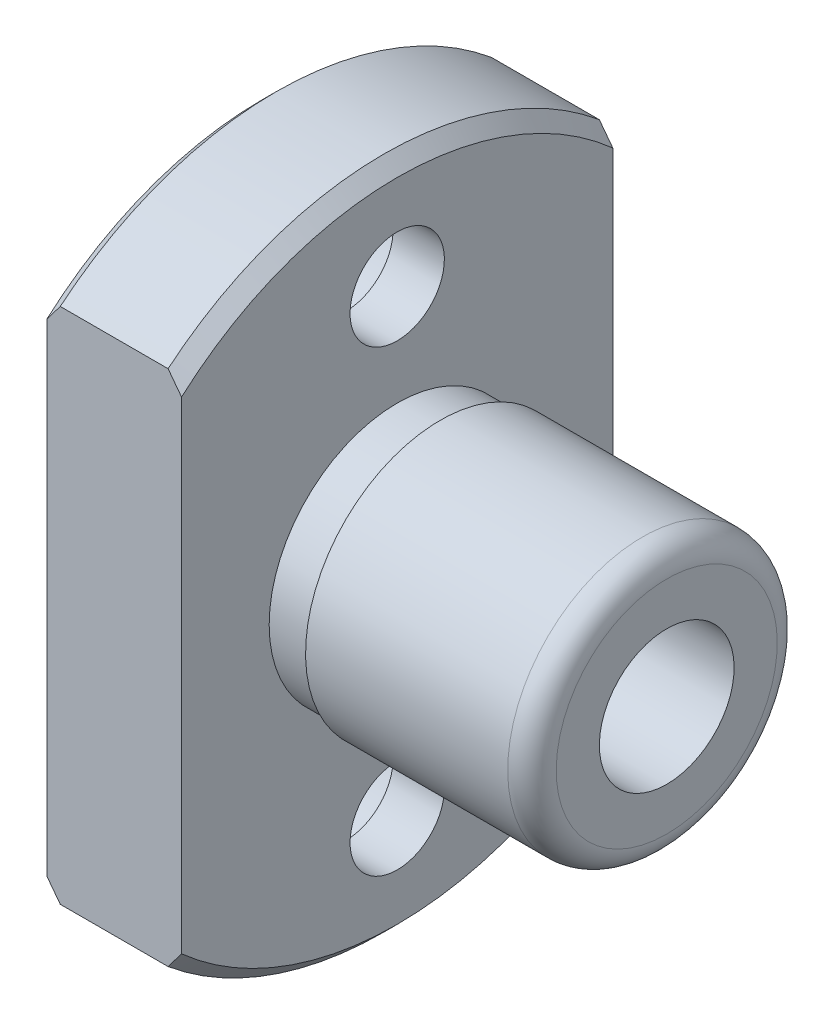
SolidWorks part; units mm, degrees
ref_plane "Front Plane" through (0, 0, 0) normal (0, 0, 1) x (1, 0, 0)
ref_plane "Top Plane" through (0, 0, 0) normal (0, 1, 0) x (1, 0, 0)
ref_plane "Right Plane" through (0, 0, 0) normal (1, 0, 0) x (0, 0, -1)
sketch "Sketch1" plane through (0, 0, 0) normal (0, 0, 1) x (1, 0, 0)
  line L0 (-5, 2.5) -> (10, 2.5)
  line L1 (-5, 2.5) -> (-5, 12.5)
  line L2 (-5, 12.5) -> (0, 12.5)
  line L3 (0, 12.5) -> (0, 4.75)
  line L4 (0, 4.75) -> (1.6, 4.75)
  line L5 (1.6, 4.75) -> (1.6, 5)
  line L6 (1.6, 5) -> (10, 5)
  line L7 (10, 5) -> (10, 2.5)
  line L8 (-5, 0) -> (10, 0) construction
  dimension "L" = 15
  dimension "D" = 10
  dimension "H" = 25
  dimension "DR_s" = 5
  dimension "T" = 5
  dimension "FIX_2" = 1.6
  dimension "FIX_1" = 0.25
revolve "Revolve1" add sketch "Sketch1" angle 360 about L8
chamfer "Chamfer1" distance 0.5 2 edges at (-5, -12.5, 0) (0, -12.5, 0)
fillet "Fillet1" radius 0.9 1 edges at (10, -5, 0)
hole_wizard "Cap Screw1" [suppressed] positions "Sketch3" profile "Sketch2" counterbore size "M2" standard "JIS"
sketch "Sketch3" plane through (-3.5, 0, 0) normal (-1, 0, 0) x (0, 0, 1)
  circle A1 centre (0, 0) radius 6.5 construction
  point P41 (0, 6.5)
  point P43 (-6.5, 0)
  point P45 (0, -6.5)
  point P47 (6.5, 0)
  dimension "P.C.D." = 17
sketch "Sketch2" plane through (-3.5, 6.5, 0) normal (0, 1, 0) x (0, 0, 1)
  line L0 (0, 0) -> (0, 10)
  line L1 (0, 10) -> (1.25, 10)
  line L3 (1.25, 10) -> (1.25, 2.1)
  line L4 (1.25, 2.1) -> (2.25, 2.1)
  line L5 (2.25, 2.1) -> (2.25, 0)
  line L7 (2.25, 0) -> (0, 0)
  line L11 (0, -6.35) -> (0, 107.95) construction
  dimension "Thru Hole Dia." = 2.5
  dimension "Thru Hole Depth" = 10
  dimension "C'Bore Dia." = 4.5
  dimension "C'Bore Depth" = 2.1
sketch "Sketch4" [suppressed] plane through (0, 0, 0) normal (-1, 0, 0) x (0, 0, 1)
  line L0 (1.1802, 9.4264) -> (9.4264, 1.1802)
  line L1 (9.4264, -1.1802) -> (1.1802, -9.4264)
  line L2 (-1.1802, -9.4264) -> (-9.4264, -1.1802)
  line L3 (-1.1802, 9.4264) -> (-9.4264, 1.1802)
  arc A0 (-1.1802, 9.4264) -> (-9.4264, 1.1802) centre (0, 0) ccw
  arc A3 (9.4264, 1.1802) -> (1.1802, 9.4264) centre (0, 0) ccw
  arc A4 (1.1802, -9.4264) -> (9.4264, -1.1802) centre (0, 0) ccw
  arc A5 (-9.4264, -1.1802) -> (-1.1802, -9.4264) centre (0, 0) ccw
  dimension "H" = 25
  dimension "W" = 15
extrude "Cut-Extrude1" [suppressed] cut sketch "Sketch4" along normal through all
sketch "Sketch5" plane through (0, 0, 0) normal (-1, 0, 0) x (0, 0, 1)
  line L0 (-8, 9.6047) -> (-8, -9.6047)
  line L1 (8, 9.6047) -> (8, -9.6047)
  arc A0 (8, -9.6047) -> (8, 9.6047) centre (0, 0) ccw
  arc A1 (-8, 9.6047) -> (-8, -9.6047) centre (0, 0) ccw
  dimension "H" = 25
  dimension "MSM_2" = 16
extrude "Cut-Extrude2" cut sketch "Sketch5" along normal through all
hole_wizard "Cap Screw2" positions "Sketch17" profile "Sketch6" counterbore size "M3" standard "JIS" end condition through all
sketch "Sketch17" plane through (-5, 0, 0) normal (-1, 0, 0) x (0, 0, 1)
  circle A1 centre (0, 0) radius 8.5 construction
  point P26 (0, 8.5)
  point P28 (0, -8.5)
  dimension "A" = 17
sketch "Sketch6" plane through (-5, -8.5, 0) normal (0, 1, 0) x (0, 0, 1)
  line L0 (0, 0) -> (0, 15)
  line L1 (0, 15) -> (1.75, 15)
  line L3 (1.75, 15) -> (1.75, 3.1)
  line L4 (1.75, 3.1) -> (3, 3.1)
  line L5 (3, 3.1) -> (3, 0)
  line L7 (3, 0) -> (0, 0)
  line L11 (0, -6.35) -> (0, 107.95) construction
  dimension "Thru Hole Dia." = 3.5
  dimension "Hole Depth" = 15
  dimension "C'Bore Dia." = 6
  dimension "C'Bore Depth" = 3.1
sketch "Sketch8" [suppressed] plane through (0, 0, 0) normal (-1, 0, 0) x (0, 0, 1)
  line L0 (17, 16.9411) -> (17, -16.9411)
  line L1 (-17, 16.9411) -> (-17, -16.9411)
  arc A0 (-17, 16.9411) -> (-17, -16.9411) centre (0, 0) ccw
  arc A1 (17, -16.9411) -> (17, 16.9411) centre (0, 0) ccw
  dimension "H" = 25
  dimension "MSM_2" = 16
extrude "Cut-Extrude3" [suppressed] cut sketch "Sketch8" along normal through all
hole_wizard "Cap Screw3" [suppressed] positions "Sketch10" profile "Sketch9" counterbore size "M4" standard "JIS"
sketch "Sketch10" [suppressed] plane through (-3.5, 0, 0) normal (-1, 0, 0) x (0, 0, 1)
  line L1 (-11, -6.5) -> (11, -6.5) construction
  line L2 (-11, -6.5) -> (-11, 6.5) construction
  line L3 (-11, 6.5) -> (11, 6.5) construction
  line L4 (11, -6.5) -> (11, 6.5) construction
  line L5 (-11, -6.5) -> (11, 6.5) construction
  line L6 (-11, 6.5) -> (11, -6.5) construction
  point P18 (11, 6.5)
  point P163 (-11, -6.5)
  point P164 (-11, 6.5)
  point P165 (11, -6.5)
  dimension "A" = 17
  dimension "F" = 22
sketch "Sketch9" [suppressed] plane through (-3.5, 6.5, 11) normal (0, 1, 0) x (0, 0, 1)
  line L0 (0, 0) -> (0, 10)
  line L1 (0, 10) -> (2.25, 10)
  line L3 (2.25, 10) -> (2.25, 4.1)
  line L4 (2.25, 4.1) -> (3.75, 4.1)
  line L5 (3.75, 4.1) -> (3.75, 0)
  line L7 (3.75, 0) -> (0, 0)
  line L11 (0, -6.35) -> (0, 107.95) construction
  dimension "Thru Hole Dia." = 4.5
  dimension "Thru Hole Depth" = 10
  dimension "C'Bore Dia." = 7.5
  dimension "C'Bore Depth" = 4.1
